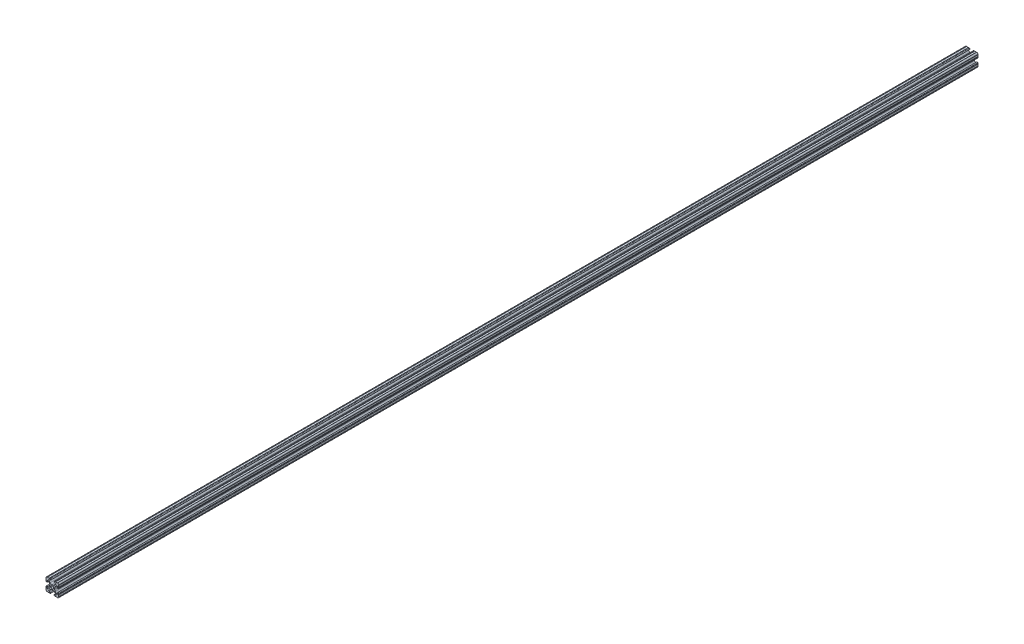
SolidWorks part; units mm, degrees
ref_plane "Front Plane" through (0, 0, 0) normal (0, 0, 1) x (1, 0, 0)
ref_plane "Top Plane" through (0, 0, 0) normal (0, 1, 0) x (1, 0, 0)
ref_plane "Right Plane" through (0, 0, 0) normal (1, 0, 0) x (0, 0, -1)
sketch "Sketch1" plane through (0, 0, 0) normal (0, 0, 1) x (1, 0, 0)
  line L0 (0, 12.7) -> (-12.7814, 12.7) construction
  line L1 (-4.5085, 0) -> (-4.5085, 2.9459)
  line L2 (-6.0437, 12.5461) -> (-10.0976, 12.6876) construction
  line L3 (-11.5616, 12.4229) -> (-4.3159, 12.1699) construction
  line L4 (-6.4364, 10.3486) -> (-6.3592, 12.5571) construction
  line L6 (-2.9459, 4.5085) -> (0, 4.5085)
  line L7 (0, 0) -> (0, 12.7) construction
  line L8 (0, 0) -> (-12.7814, 0) construction
  line L9 (0.7813, 0.7813) -> (-0.7813, -0.7813) construction
  line L10 (-2.9459, 4.5085) -> (-7.1484, 8.711)
  line L11 (-4.5085, 2.9459) -> (-8.711, 7.1484)
  line L13 (0, 0) -> (-12.7814, 12.7814) construction
  line L14 (-10.4131, 12.6987) -> (-4.3048, 12.4853)
  line L15 (-4.3048, 12.4853) -> (-4.382, 10.2769) construction
  line L16 (-4.382, 10.2769) -> (-6.4364, 10.3486)
  line L17 (-12.6987, 10.4131) -> (-12.4853, 4.3048)
  line L18 (-10.2769, 4.382) -> (-10.3486, 6.4364)
  circle A0 centre (0, 0) radius 2.6035
  arc A1 (-4.382, 10.2769) -> (-4.3048, 12.4853) centre (-4.3434, 11.3811) ccw
  arc A2 (-7.1484, 8.711) -> (-6.4364, 10.3486) centre (-6.4698, 9.3896) cw
  arc A3 (-8.711, 7.1484) -> (-10.3486, 6.4364) centre (-9.3896, 6.4698) ccw
  arc A4 (-10.2769, 4.382) -> (-12.4853, 4.3048) centre (-11.3811, 4.3434) cw
  arc A5 (-10.4131, 12.6987) -> (-12.6987, 10.4131) centre (-10.4902, 10.4902) ccw
  arc A6 (-10.4131, 12.6987) -> (-9.7821, 12.6766) centre (-10.0976, 12.6876) ccw
  arc A7 (-6.3592, 12.5571) -> (-5.7282, 12.5351) centre (-6.0437, 12.5461) ccw
  arc A8 (-12.5571, 6.3592) -> (-12.5351, 5.7282) centre (-12.5461, 6.0437) cw
  arc A9 (-12.6987, 10.4131) -> (-12.6766, 9.7821) centre (-12.6876, 10.0976) cw
  dimension "D1" = 5.207
  dimension "D5" = 14.859
  dimension "D9" = 2
  dimension "D2" = 25.4
  dimension "D12" = 0.6314
  dimension "D10" = 2.2098
  dimension "D3" = 9.017
  dimension "D4" = 9.017
  dimension "D6" = 25.4
  dimension "D7" = 6.477
  dimension "D8" = 2.2098
  dimension "D11" = 12.7
sketch "Sketch3" plane through (0, 0, 0) normal (0, 0, 1) x (1, 0, 0)
  line L0 (-2.9459, 4.5085) -> (0, 4.5085) construction
  line L1 (-2.9459, 4.5085) -> (-7.1484, 8.711) construction
  line L2 (-4.382, 10.2769) -> (-6.4364, 10.3486) construction
  line L3 (-10.4131, 12.6987) -> (-4.3048, 12.4853) construction
  line L4 (-4.5085, 0) -> (-4.5085, 2.9459) construction
  line L5 (-4.5085, 2.9459) -> (-8.711, 7.1484) construction
  line L6 (-10.2769, 4.382) -> (-10.3486, 6.4364) construction
  line L7 (-12.6987, 10.4131) -> (-12.4853, 4.3048) construction
  line L8 (-1.1153, 4.5085) -> (1.1153, 4.5085)
  line L9 (-4.2404, 5.803) -> (-7.1484, 8.711)
  line L10 (-4.382, 10.2769) -> (-6.4364, 10.3486)
  line L11 (-9.7821, 12.6766) -> (-6.3592, 12.5571)
  line L12 (-4.5085, -1.1153) -> (-4.5085, 1.1153)
  line L13 (-5.803, 4.2404) -> (-8.711, 7.1484)
  line L14 (-10.2769, 4.382) -> (-10.3486, 6.4364)
  line L15 (-12.6766, 9.7821) -> (-12.5571, 6.3592)
  line L16 (-5.7282, 12.5351) -> (-4.3048, 12.4853)
  line L17 (-12.5351, 5.7282) -> (-12.4853, 4.3048)
  line L18 (0, 0) -> (0, 12.7) construction
  line L19 (0, 0) -> (-12.7814, 0) construction
  line L20 (12.5351, 5.7282) -> (12.4853, 4.3048)
  line L21 (5.7282, 12.5351) -> (4.3048, 12.4853)
  line L22 (12.6766, 9.7821) -> (12.5571, 6.3592)
  line L23 (10.2769, 4.382) -> (10.3486, 6.4364)
  line L24 (5.803, 4.2404) -> (8.711, 7.1484)
  line L25 (4.5085, -1.1153) -> (4.5085, 1.1153)
  line L26 (9.7821, 12.6766) -> (6.3592, 12.5571)
  line L27 (4.382, 10.2769) -> (6.4364, 10.3486)
  line L28 (4.2404, 5.803) -> (7.1484, 8.711)
  line L29 (4.2404, -5.803) -> (7.1484, -8.711)
  line L30 (4.382, -10.2769) -> (6.4364, -10.3486)
  line L31 (9.7821, -12.6766) -> (6.3592, -12.5571)
  line L32 (5.803, -4.2404) -> (8.711, -7.1484)
  line L33 (10.2769, -4.382) -> (10.3486, -6.4364)
  line L34 (12.6766, -9.7821) -> (12.5571, -6.3592)
  line L35 (5.7282, -12.5351) -> (4.3048, -12.4853)
  line L36 (12.5351, -5.7282) -> (12.4853, -4.3048)
  line L37 (-12.5351, -5.7282) -> (-12.4853, -4.3048)
  line L38 (-5.7282, -12.5351) -> (-4.3048, -12.4853)
  line L39 (-12.6766, -9.7821) -> (-12.5571, -6.3592)
  line L40 (-10.2769, -4.382) -> (-10.3486, -6.4364)
  line L41 (-5.803, -4.2404) -> (-8.711, -7.1484)
  line L42 (-9.7821, -12.6766) -> (-6.3592, -12.5571)
  line L43 (-4.382, -10.2769) -> (-6.4364, -10.3486)
  line L44 (-4.2404, -5.803) -> (-7.1484, -8.711)
  line L45 (-1.1153, -4.5085) -> (1.1153, -4.5085)
  arc A0 (-10.4131, 12.6987) -> (-9.7821, 12.6766) centre (-10.0976, 12.6876) ccw construction
  arc A1 (-6.4364, 10.3486) -> (-7.1484, 8.711) centre (-6.4698, 9.3896) ccw construction
  arc A2 (-4.382, 10.2769) -> (-4.3048, 12.4853) centre (-4.3434, 11.3811) ccw construction
  arc A3 (-8.711, 7.1484) -> (-10.3486, 6.4364) centre (-9.3896, 6.4698) ccw construction
  arc A4 (-12.4853, 4.3048) -> (-10.2769, 4.382) centre (-11.3811, 4.3434) ccw construction
  arc A5 (-6.3592, 12.5571) -> (-5.7282, 12.5351) centre (-6.0437, 12.5461) ccw construction
  arc A6 (-10.4131, 12.6987) -> (-12.6987, 10.4131) centre (-10.4902, 10.4902) ccw construction
  arc A7 (-12.6766, 9.7821) -> (-12.6987, 10.4131) centre (-12.6876, 10.0976) ccw construction
  arc A8 (-12.5351, 5.7282) -> (-12.5571, 6.3592) centre (-12.5461, 6.0437) ccw construction
  arc A9 (-10.4131, 12.6987) -> (-9.7821, 12.6766) centre (-10.0976, 12.6876) ccw
  arc A10 (-6.4364, 10.3486) -> (-7.1484, 8.711) centre (-6.4698, 9.3896) ccw
  arc A11 (-4.382, 10.2769) -> (-4.3048, 12.4853) centre (-4.3434, 11.3811) ccw
  arc A12 (-8.711, 7.1484) -> (-10.3486, 6.4364) centre (-9.3896, 6.4698) ccw
  arc A13 (-12.4853, 4.3048) -> (-10.2769, 4.382) centre (-11.3811, 4.3434) ccw
  arc A14 (-6.3592, 12.5571) -> (-5.7282, 12.5351) centre (-6.0437, 12.5461) ccw
  arc A15 (-10.4131, 12.6987) -> (-12.6987, 10.4131) centre (-10.4902, 10.4902) ccw
  arc A16 (-12.6766, 9.7821) -> (-12.6987, 10.4131) centre (-12.6876, 10.0976) ccw
  arc A17 (-12.5351, 5.7282) -> (-12.5571, 6.3592) centre (-12.5461, 6.0437) ccw
  arc A18 (-1.1153, 4.5085) -> (-4.2404, 5.803) centre (-1.1153, 8.9281) cw
  arc A19 (4.5085, 1.1153) -> (5.803, 4.2404) centre (8.9281, 1.1153) cw
  arc A20 (1.1153, 4.5085) -> (4.2404, 5.803) centre (1.1153, 8.9281) ccw
  arc A21 (-4.5085, 1.1153) -> (-5.803, 4.2404) centre (-8.9281, 1.1153) ccw
  arc A22 (12.5351, 5.7282) -> (12.5571, 6.3592) centre (12.5461, 6.0437) cw
  arc A23 (12.6766, 9.7821) -> (12.6987, 10.4131) centre (12.6876, 10.0976) cw
  arc A24 (10.4131, 12.6987) -> (12.6987, 10.4131) centre (10.4902, 10.4902) cw
  arc A25 (6.3592, 12.5571) -> (5.7282, 12.5351) centre (6.0437, 12.5461) cw
  arc A26 (12.4853, 4.3048) -> (10.2769, 4.382) centre (11.3811, 4.3434) cw
  arc A27 (8.711, 7.1484) -> (10.3486, 6.4364) centre (9.3896, 6.4698) cw
  arc A28 (4.382, 10.2769) -> (4.3048, 12.4853) centre (4.3434, 11.3811) cw
  arc A29 (6.4364, 10.3486) -> (7.1484, 8.711) centre (6.4698, 9.3896) cw
  arc A30 (10.4131, 12.6987) -> (9.7821, 12.6766) centre (10.0976, 12.6876) cw
  arc A31 (10.4131, -12.6987) -> (9.7821, -12.6766) centre (10.0976, -12.6876) ccw
  arc A32 (6.4364, -10.3486) -> (7.1484, -8.711) centre (6.4698, -9.3896) ccw
  arc A33 (4.382, -10.2769) -> (4.3048, -12.4853) centre (4.3434, -11.3811) ccw
  arc A34 (8.711, -7.1484) -> (10.3486, -6.4364) centre (9.3896, -6.4698) ccw
  arc A35 (12.4853, -4.3048) -> (10.2769, -4.382) centre (11.3811, -4.3434) ccw
  arc A36 (6.3592, -12.5571) -> (5.7282, -12.5351) centre (6.0437, -12.5461) ccw
  arc A37 (10.4131, -12.6987) -> (12.6987, -10.4131) centre (10.4902, -10.4902) ccw
  arc A38 (12.6766, -9.7821) -> (12.6987, -10.4131) centre (12.6876, -10.0976) ccw
  arc A39 (12.5351, -5.7282) -> (12.5571, -6.3592) centre (12.5461, -6.0437) ccw
  arc A40 (-4.5085, -1.1153) -> (-5.803, -4.2404) centre (-8.9281, -1.1153) cw
  arc A41 (1.1153, -4.5085) -> (4.2404, -5.803) centre (1.1153, -8.9281) cw
  arc A42 (4.5085, -1.1153) -> (5.803, -4.2404) centre (8.9281, -1.1153) ccw
  arc A43 (-1.1153, -4.5085) -> (-4.2404, -5.803) centre (-1.1153, -8.9281) ccw
  arc A44 (-12.5351, -5.7282) -> (-12.5571, -6.3592) centre (-12.5461, -6.0437) cw
  arc A45 (-12.6766, -9.7821) -> (-12.6987, -10.4131) centre (-12.6876, -10.0976) cw
  arc A46 (-10.4131, -12.6987) -> (-12.6987, -10.4131) centre (-10.4902, -10.4902) cw
  arc A47 (-6.3592, -12.5571) -> (-5.7282, -12.5351) centre (-6.0437, -12.5461) cw
  arc A48 (-12.4853, -4.3048) -> (-10.2769, -4.382) centre (-11.3811, -4.3434) cw
  arc A49 (-8.711, -7.1484) -> (-10.3486, -6.4364) centre (-9.3896, -6.4698) cw
  arc A50 (-4.382, -10.2769) -> (-4.3048, -12.4853) centre (-4.3434, -11.3811) cw
  arc A51 (-6.4364, -10.3486) -> (-7.1484, -8.711) centre (-6.4698, -9.3896) cw
  arc A52 (-10.4131, -12.6987) -> (-9.7821, -12.6766) centre (-10.0976, -12.6876) cw
  circle A53 centre (0, 0) radius 2.6035 construction
  circle A54 centre (0, 0) radius 2.6035
  point P135 (4.5085, 0)
  dimension "D2" = 4.4196
extrude "Extrude1" add sketch "Sketch3" along normal mid plane 1828.8
equation "\"D10@Sketch1\" = \"D8@Sketch1\""
equation "\"D11@Sketch1\" = \"D6@Sketch1\"/2"
equation "\"D12@Sketch1\" = \"D8@Sketch1\"/3.5"
equation "\"D2@Sketch3\" = \"D8@Sketch1\"*2"
